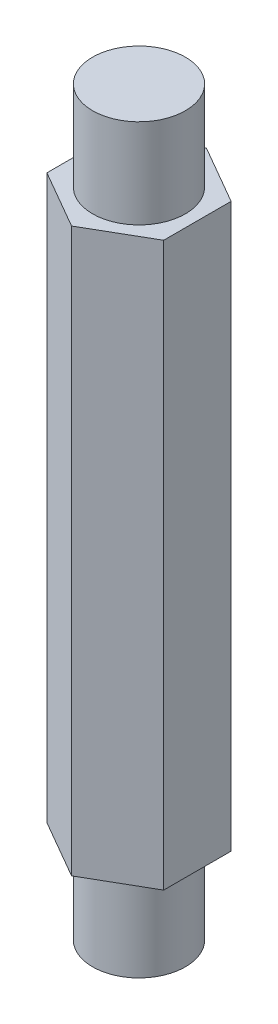
SolidWorks part; units mm, degrees
ref_plane "Front Plane" through (0, 0, 0) normal (0, 0, 1) x (1, 0, 0)
ref_plane "Top Plane" through (0, 0, 0) normal (0, 1, 0) x (1, 0, 0)
ref_plane "Right Plane" through (0, 0, 0) normal (1, 0, 0) x (0, 0, -1)
sketch "Sketch1" plane through (0, 0, 0) normal (0, 1, 0) x (1, 0, 0)
  line L1 (0, -2.396) -> (2.075, -1.198)
  line L2 (2.075, -1.198) -> (2.075, 1.198)
  line L3 (2.075, 1.198) -> (0, 2.396)
  line L4 (0, 2.396) -> (-2.075, 1.198)
  line L5 (-2.075, 1.198) -> (-2.075, -1.198)
  line L6 (-2.075, -1.198) -> (0, -2.396)
  circle A0 centre (0, 0) radius 1.65
  circle A1 centre (0, 0) radius 2.075 construction
  dimension "D1" = 3.3
  dimension "D2" = 4.15
extrude "Boss-Extrude1" add sketch "Sketch1" along normal blind 20
sketch "Sketch2" plane through (0, 0, 0) normal (0, -1, 0) x (1, 0, 0)
  circle A0 centre (0, 0) radius 1.65
extrude "Boss-Extrude2" add sketch "Sketch2" along normal blind 3.175 separate body
sketch "Sketch3" plane through (0, 20, 0) normal (0, 1, 0) x (1, 0, 0)
  circle A0 centre (0, 0) radius 1.65
extrude "Boss-Extrude3" add sketch "Sketch3" along normal blind 3.175 separate body
